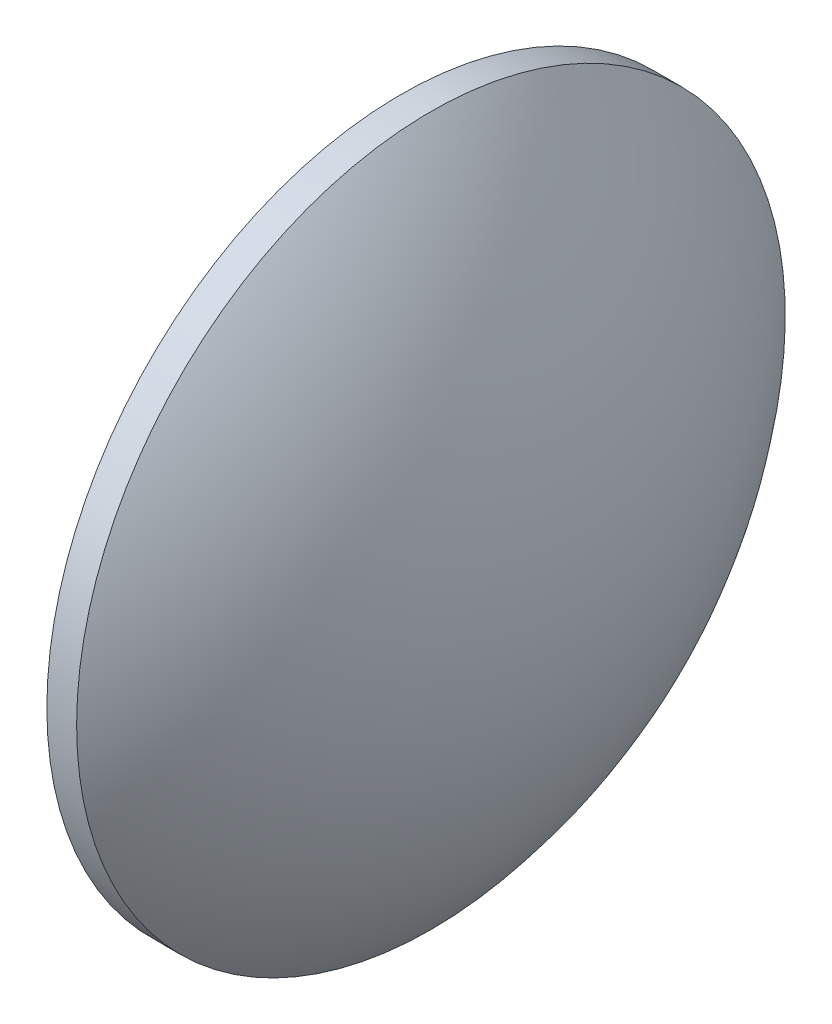
SolidWorks part; units mm, degrees
ref_plane "前视基准面" through (0, 0, 0) normal (0, 0, 1) x (1, 0, 0)
ref_plane "上视基准面" through (0, 0, 0) normal (0, 1, 0) x (1, 0, 0)
ref_plane "右视基准面" through (0, 0, 0) normal (1, 0, 0) x (0, 0, -1)
sketch "草图1" plane through (0, 0, 0) normal (0, 0, 1) x (1, 0, 0)
  line L0 (439.8966, 82.5986) -> (449.4924, 82.5986) construction
  line L1 (441.5199, 82.5986) -> (441.5199, 92.5986)
  line L2 (441.5199, 92.5986) -> (442.3599, 92.5986)
  line L3 (446.0199, 82.5986) -> (441.5199, 82.5986)
  arc A0 (446.0199, 82.5986) -> (442.3599, 92.5986) centre (430.5287, 82.5986) ccw
revolve "旋转1" add sketch "草图1" angle 360 about L0
